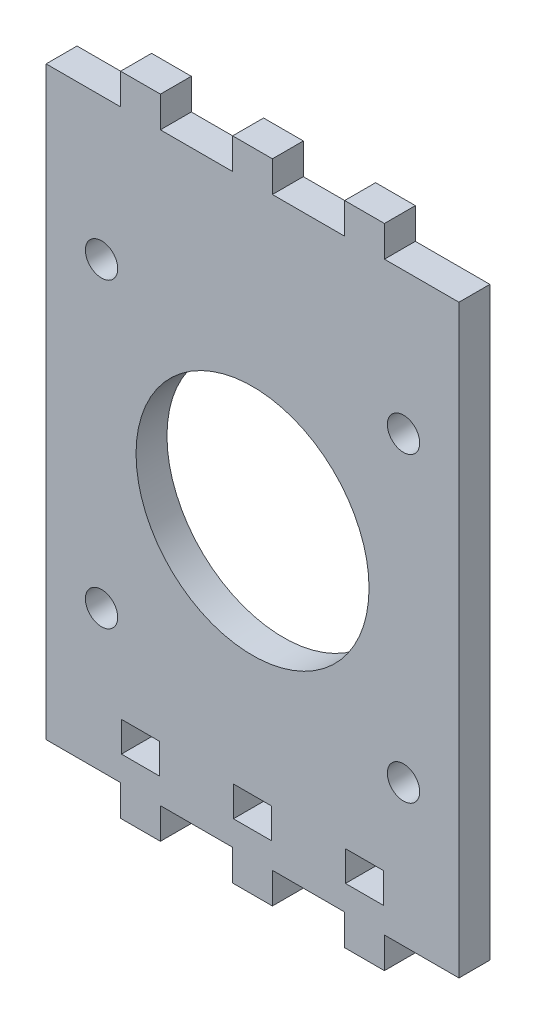
SolidWorks part; units mm, degrees
ref_plane "Front Plane" through (0, 0, 0) normal (0, 0, 1) x (1, 0, 0)
ref_plane "Top Plane" through (0, 0, 0) normal (0, 1, 0) x (1, 0, 0)
ref_plane "Right Plane" through (0, 0, 0) normal (1, 0, 0) x (0, 0, -1)
sketch "Sketch1" plane through (0, 0, 0) normal (0, 0, 1) x (1, 0, 0)
  line L0 (-2, -30) -> (-2, -33.175)
  line L3 (-13.5, -30) -> (13.5, -30)
  line L5 (-13.5, -30) -> (-9.5, -30)
  line L6 (-13.5, -30) -> (-13.5, -33.175)
  line L7 (-13.5, -33.175) -> (-9.5, -33.175)
  line L8 (-9.5, -30) -> (-9.5, -33.175)
  line L9 (13.5, -30) -> (9.5, -30)
  line L10 (13.5, -30) -> (13.5, -33.175)
  line L11 (13.5, -33.175) -> (9.5, -33.175)
  line L12 (9.5, -30) -> (9.5, -33.175)
  line L13 (-2, -30) -> (2, -30)
  line L14 (-2, -33.175) -> (2, -33.175)
  line L15 (2, -30) -> (2, -33.175)
  line L16 (-2, -30) -> (2, -33.175) construction
  line L17 (-2, -33.175) -> (2, -30) construction
  line L18 (-21.15, 21.15) -> (21.15, 21.15) construction
  line L19 (21.15, -30) -> (-21.15, -30)
  line L20 (21.15, -30) -> (21.15, 30)
  line L21 (21.15, 30) -> (-21.15, 30)
  line L22 (-21.15, -30) -> (-21.15, 30)
  line L23 (-21.15, 0) -> (21.15, 0) construction
  line L24 (-2, 33.175) -> (2, 30) construction
  line L25 (-2, 30) -> (2, 33.175) construction
  line L26 (2, 30) -> (2, 33.175)
  line L27 (-2, 33.175) -> (2, 33.175)
  line L28 (9.5, 30) -> (9.5, 33.175)
  line L29 (13.5, 33.175) -> (9.5, 33.175)
  line L30 (13.5, 30) -> (13.5, 33.175)
  line L31 (-9.5, 30) -> (-9.5, 33.175)
  line L32 (-13.5, 33.175) -> (-9.5, 33.175)
  line L33 (-13.5, 30) -> (-13.5, 33.175)
  line L34 (-2, 30) -> (-2, 33.175)
  line L35 (-13.5, 31.5875) -> (13.5, 31.5875)
  line L37 (0, -21.15) -> (0, -30) construction
  line L38 (-2, -21.15) -> (2, -24.325) construction
  line L39 (21.15, -27.1625) -> (-21.15, -27.1625) construction
  line L40 (-2, -24.325) -> (2, -21.15) construction
  line L41 (2, -27.5) -> (2, -24.325)
  line L43 (9.5, -27.5) -> (9.5, -24.325)
  line L45 (13.5, -27.5) -> (13.5, -24.325)
  line L46 (-9.5, -27.5) -> (-9.5, -24.325)
  line L48 (-13.5, -27.5) -> (-13.5, -24.325)
  line L49 (-2, -27.5) -> (-2, -24.325)
  line L50 (-13.5, -24.325) -> (-9.5, -24.325)
  line L51 (-2, -24.325) -> (2, -24.325)
  line L52 (9.5, -24.325) -> (13.5, -24.325)
  line L54 (-2, -24.325) -> (2, -27.5) construction
  line L56 (-2, -27.5) -> (2, -24.325) construction
  line L57 (0, -27.5) -> (0, -18.65) construction
  line L58 (-2, -27.5) -> (2, -27.5)
  line L59 (-13.5, -27.5) -> (-9.5, -27.5)
  line L60 (13.5, -27.5) -> (9.5, -27.5)
  line L61 (-2, -27.5) -> (2, -27.5)
  line L62 (-13.5, -27.5) -> (-9.5, -27.5)
  circle A0 centre (-15.5, 15.5) radius 1.7
  circle A1 centre (15.5, 15.5) radius 1.7
  circle A2 centre (15.5, -15.5) radius 1.7
  circle A3 centre (-15.5, -15.5) radius 1.7
  circle A4 centre (0, 0) radius 12
  point P17 (-21.15, 21.15)
  point P25 (21.15, 21.15)
  point P33 (0, -31.5875)
  point P40 (0, -30)
  point P47 (0, 31.5875)
  point P51 (0, 31.5875)
  point P69 (0, -22.7375)
  point P78 (0, -25.9125)
  dimension "D5" = 3.4
  dimension "D10" = 24
  dimension "D1" = 42.3
  dimension "D12" = 4
  dimension "D13" = 3.175
  dimension "D16" = 42.3
  dimension "D3" = 5.65
  dimension "D2" = 51.15
  dimension "D4" = 30
  dimension "D6" = 21.15
  dimension "D7" = 5.65
  dimension "D11" = 60
  dimension "D14" = 7.5
  dimension "D8" = 2
  dimension "D9" = 2
extrude "Boss-Extrude1" add sketch "Sketch1" along normal blind 3.175 contours L22 L19 L3 L20 L21 A4 A3 A2 A1 A0 L59 L48 L50 L46 L58 L49 L51 L41 L45 L60 L43 L52 | L33 L35 L31 L32 | L35 L33 L21 L31 | L28 L35 L30 L29 | L35 L28 L21 L30 | L35 L34 L21 L26 | L34 L35 L26 L27 | L8 L3 L6 L7 | L15 L3 L0 L14 | L3 L12 L11 L10
sketch "Sketch2" plane through (0, 0, 3.175) normal (0, 0, 1) x (1, 0, 0)
  line L14 (13.4594, -27.4594) -> (13.4594, -24.3656)
  line L15 (9.5406, -27.4594) -> (13.4594, -27.4594)
  line L16 (9.5406, -24.3656) -> (9.5406, -27.4594)
  line L17 (13.4594, -24.3656) -> (9.5406, -24.3656)
  line L18 (13.4594, -27.4594) -> (13.4594, -24.3656)
  line L19 (9.5406, -27.4594) -> (13.4594, -27.4594)
  line L20 (9.5406, -24.3656) -> (9.5406, -27.4594)
  line L21 (13.4594, -24.3656) -> (9.5406, -24.3656)
  line L32 (1.9594, -27.4594) -> (1.9594, -24.3656)
  line L33 (-1.9594, -27.4594) -> (1.9594, -27.4594)
  line L34 (-1.9594, -24.3656) -> (-1.9594, -27.4594)
  line L35 (1.9594, -24.3656) -> (-1.9594, -24.3656)
  line L36 (1.9594, -27.4594) -> (1.9594, -24.3656)
  line L37 (-1.9594, -27.4594) -> (1.9594, -27.4594)
  line L38 (-1.9594, -24.3656) -> (-1.9594, -27.4594)
  line L39 (1.9594, -24.3656) -> (-1.9594, -24.3656)
  line L50 (-9.5406, -27.4594) -> (-9.5406, -24.3656)
  line L51 (-13.4594, -27.4594) -> (-9.5406, -27.4594)
  line L52 (-13.4594, -24.3656) -> (-13.4594, -27.4594)
  line L53 (-9.5406, -24.3656) -> (-13.4594, -24.3656)
  line L54 (-9.5406, -27.4594) -> (-9.5406, -24.3656)
  line L55 (-13.4594, -27.4594) -> (-9.5406, -27.4594)
  line L56 (-13.4594, -24.3656) -> (-13.4594, -27.4594)
  line L57 (-9.5406, -24.3656) -> (-13.4594, -24.3656)
  line L168 (-21.1906, 30.0406) -> (-21.1906, -30.0406)
  line L169 (-21.1906, -30.0406) -> (-13.5406, -30.0406)
  line L170 (-13.5406, -30.0406) -> (-13.5406, -33.2156)
  line L171 (-13.5406, -33.2156) -> (-9.4594, -33.2156)
  line L172 (-9.4594, -33.2156) -> (-9.4594, -30.0406)
  line L173 (-9.4594, -30.0406) -> (-2.0406, -30.0406)
  line L174 (-2.0406, -30.0406) -> (-2.0406, -33.2156)
  line L175 (-2.0406, -33.2156) -> (2.0406, -33.2156)
  line L176 (2.0406, -33.2156) -> (2.0406, -30.0406)
  line L177 (2.0406, -30.0406) -> (9.4594, -30.0406)
  line L178 (9.4594, -30.0406) -> (9.4594, -33.2156)
  line L179 (9.4594, -33.2156) -> (13.5406, -33.2156)
  line L180 (13.5406, -33.2156) -> (13.5406, -30.0406)
  line L181 (13.5406, -30.0406) -> (21.1906, -30.0406)
  line L182 (21.1906, -30.0406) -> (21.1906, 30.0406)
  line L183 (21.1906, 30.0406) -> (13.5406, 30.0406)
  line L184 (13.5406, 30.0406) -> (13.5406, 33.2156)
  line L185 (13.5406, 33.2156) -> (9.4594, 33.2156)
  line L186 (9.4594, 33.2156) -> (9.4594, 30.0406)
  line L187 (9.4594, 30.0406) -> (2.0406, 30.0406)
  line L188 (2.0406, 30.0406) -> (2.0406, 33.2156)
  line L189 (2.0406, 33.2156) -> (-2.0406, 33.2156)
  line L190 (-2.0406, 33.2156) -> (-2.0406, 30.0406)
  line L191 (-2.0406, 30.0406) -> (-9.4594, 30.0406)
  line L192 (-9.4594, 30.0406) -> (-9.4594, 33.2156)
  line L193 (-9.4594, 33.2156) -> (-13.5406, 33.2156)
  line L194 (-13.5406, 33.2156) -> (-13.5406, 30.0406)
  line L195 (-13.5406, 30.0406) -> (-21.1906, 30.0406)
  line L196 (-21.1906, 30.0406) -> (-21.1906, -30.0406)
  line L197 (-21.1906, -30.0406) -> (-13.5406, -30.0406)
  line L198 (-13.5406, -30.0406) -> (-13.5406, -33.2156)
  line L199 (-13.5406, -33.2156) -> (-9.4594, -33.2156)
  line L200 (-9.4594, -33.2156) -> (-9.4594, -30.0406)
  line L201 (-9.4594, -30.0406) -> (-2.0406, -30.0406)
  line L202 (-2.0406, -30.0406) -> (-2.0406, -33.2156)
  line L203 (-2.0406, -33.2156) -> (2.0406, -33.2156)
  line L204 (2.0406, -33.2156) -> (2.0406, -30.0406)
  line L205 (2.0406, -30.0406) -> (9.4594, -30.0406)
  line L206 (9.4594, -30.0406) -> (9.4594, -33.2156)
  line L207 (9.4594, -33.2156) -> (13.5406, -33.2156)
  line L208 (13.5406, -33.2156) -> (13.5406, -30.0406)
  line L209 (13.5406, -30.0406) -> (21.1906, -30.0406)
  line L210 (21.1906, -30.0406) -> (21.1906, 30.0406)
  line L211 (21.1906, 30.0406) -> (13.5406, 30.0406)
  line L212 (13.5406, 30.0406) -> (13.5406, 33.2156)
  line L213 (13.5406, 33.2156) -> (9.4594, 33.2156)
  line L214 (9.4594, 33.2156) -> (9.4594, 30.0406)
  line L215 (9.4594, 30.0406) -> (2.0406, 30.0406)
  line L216 (2.0406, 30.0406) -> (2.0406, 33.2156)
  line L217 (2.0406, 33.2156) -> (-2.0406, 33.2156)
  line L218 (-2.0406, 33.2156) -> (-2.0406, 30.0406)
  line L219 (-2.0406, 30.0406) -> (-9.4594, 30.0406)
  line L220 (-9.4594, 30.0406) -> (-9.4594, 33.2156)
  line L221 (-9.4594, 33.2156) -> (-13.5406, 33.2156)
  line L222 (-13.5406, 33.2156) -> (-13.5406, 30.0406)
  line L223 (-13.5406, 30.0406) -> (-21.1906, 30.0406)
  circle A2 centre (0, 0) radius 11.9594
  circle A3 centre (0, 0) radius 11.9594
  circle A399 centre (-15.5, -15.5) radius 1.6594
  circle A400 centre (-15.5, -15.5) radius 1.6594
  circle A402 centre (15.5, -15.5) radius 1.6594
  circle A403 centre (15.5, -15.5) radius 1.6594
  circle A410 centre (15.5, 15.5) radius 1.6594
  circle A411 centre (15.5, 15.5) radius 1.6594
  circle A413 centre (-15.5, 15.5) radius 1.6594
  circle A414 centre (-15.5, 15.5) radius 1.6594
  dimension "D1" = 0.0406
  dimension "D2" = 0.0406
  dimension "D3" = 0.0406
  dimension "D4" = 0.0406
  dimension "D5" = 0.0406
  dimension "D6" = 0.0406
  dimension "D7" = 0.0406
  dimension "D8" = 0.0406
  dimension "D9" = 0.0406
extrude "Boss-Extrude2" add sketch "Sketch2" against normal blind 3.175
equation "\"stepper width\"=4.23"
equation "\"D1@Sketch1\"=\"stepper width\""
equation "\"stepper hole disctance\"= 3.1"
equation "\"stepper hole diameter\"=0.34"
equation "\"D5@Sketch1\"=\"stepper hole diameter\""
equation "\"stepper shaft hole\"=2.4"
equation "\"D10@Sketch1\"=\"stepper shaft hole\""
equation "\"tooth width\"=0.4"
equation "\"D12@Sketch1\"=\"tooth width\""
equation "\"tooth thickness\"=0.3175"
equation "\"D13@Sketch1\"=\"tooth thickness\""
equation "\"tooth to side\"=0.75"
equation "\"D16@Sketch1\"=\"stepper width\""
equation "\"D3@Sketch1\"=(\"stepper width\"-\"stepper hole disctance\")/2"
equation "\"D2@Sketch1\"=\"stepper width\" + 3 - (\"stepper width\"/2)"
equation "\"D6@Sketch1\"=\"stepper width\"/2"
equation "\"D7@Sketch1\"=(\"stepper width\"-\"stepper hole disctance\")/2"
equation "\"motor chamber height\"=8.55627"
equation "\"D1@Boss-Extrude1\"=\"tooth thickness\""
equation "\"D14@Sketch1\"=.75"
